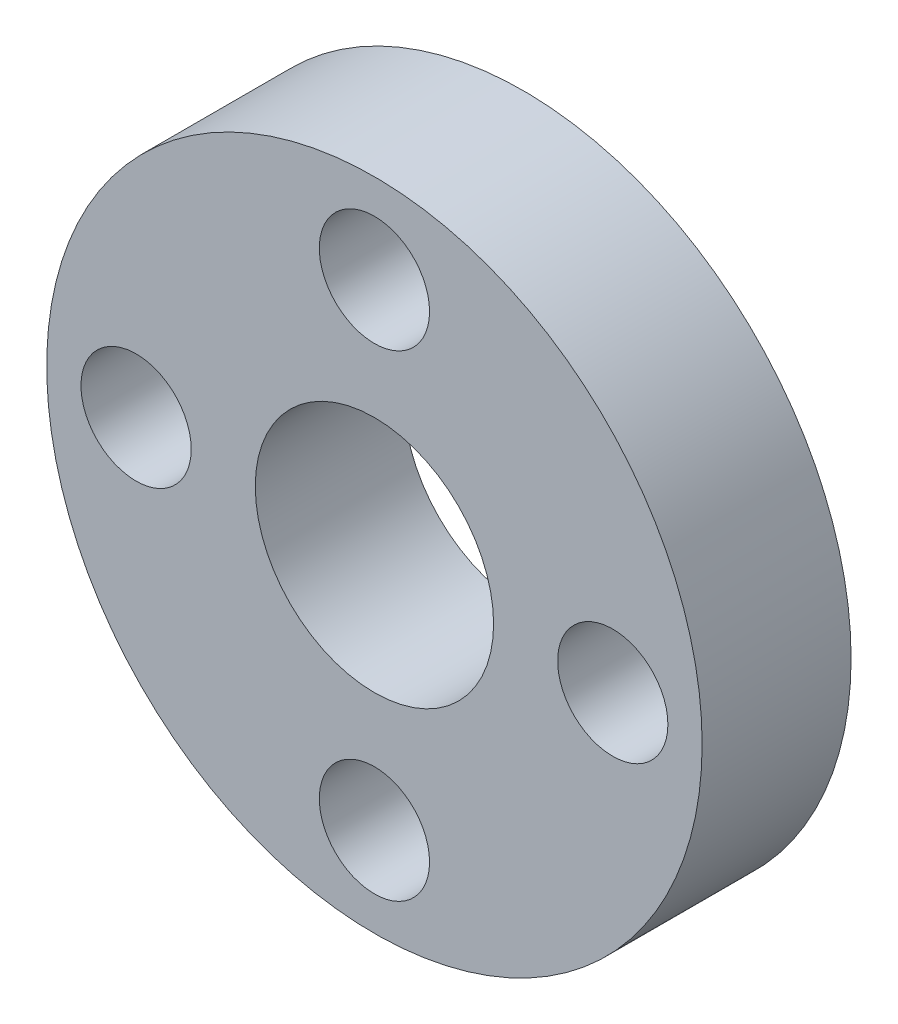
SolidWorks part; units mm, degrees
material "2024 Alloy"
ref_plane "Front Plane" through (0, 0, 0) normal (0, 0, 1) x (1, 0, 0)
ref_plane "Top Plane" through (0, 0, 0) normal (0, 1, 0) x (1, 0, 0)
ref_plane "Right Plane" through (0, 0, 0) normal (1, 0, 0) x (0, 0, -1)
sketch "Sketch1" plane through (0, 0, 0) normal (0, 0, 1) x (1, 0, 0)
  circle A0 centre (0, 0) radius 11
  circle A1 centre (0, 0) radius 4
  circle A2 centre (0, 8) radius 1.85
  circle A3 centre (0, 0) radius 11
  circle A4 centre (8, 0) radius 1.85
  circle A5 centre (0, 0) radius 11
  circle A6 centre (0, -8) radius 1.85
  circle A7 centre (0, 0) radius 11
  circle A8 centre (-8, 0) radius 1.85
  point P18 (0, 0)
  dimension "D1" = 8
  dimension "D2" = 3.7
  dimension "D4" = 22
  dimension "D3" = 8
  dimension "D5" = 4
extrude "Boss-Extrude1" add sketch "Sketch1" along normal blind 5 contours A0 A8 A6 A4 A2 A1
